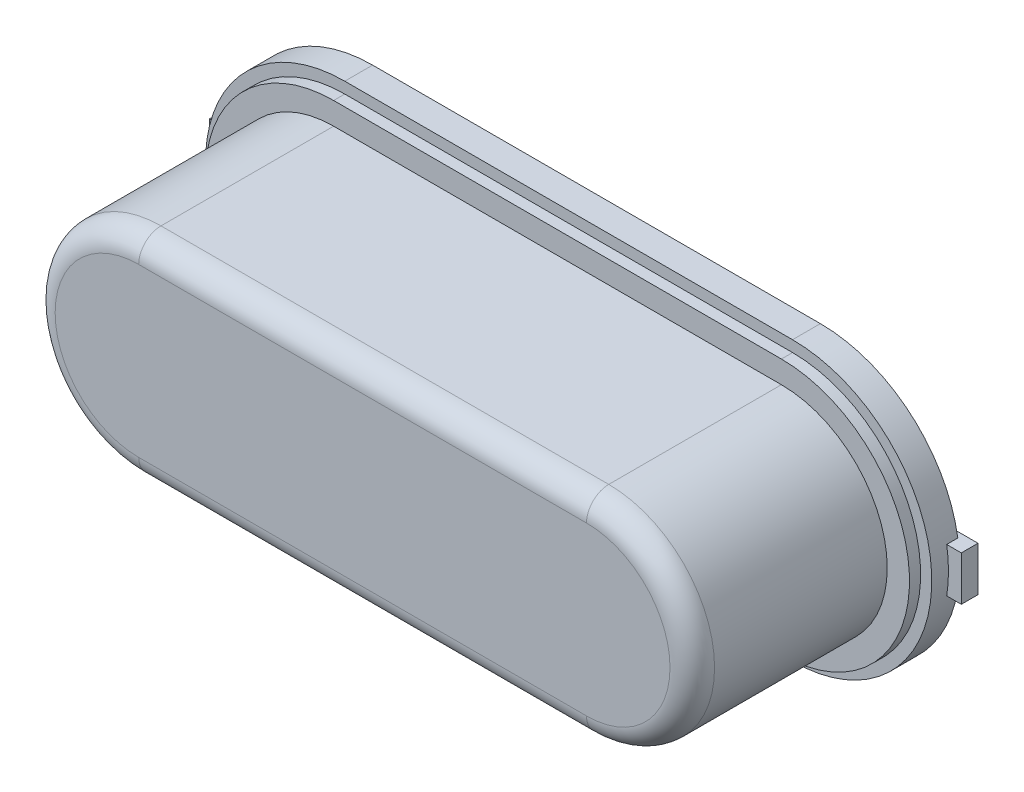
SolidWorks part; units mm, degrees
material "1023 Carbon Steel Sheet (SS)"
ref_plane "Front Plane" through (0, 0, 0) normal (0, 0, 1) x (1, 0, 0)
ref_plane "Top Plane" through (0, 0, 0) normal (0, 1, 0) x (1, 0, 0)
ref_plane "Right Plane" through (0, 0, 0) normal (1, 0, 0) x (0, 0, -1)
sketch "Sketch1" plane through (0, 0, 0) normal (0, 0, 1) x (1, 0, 0)
  line L0 (-4.02, 0) -> (4.02, 0) construction
  line L1 (-4.02, 2.5) -> (4.02, 2.5)
  line L2 (-4.02, -2.5) -> (4.02, -2.5)
  arc A0 (-4.02, 2.5) -> (-4.02, -2.5) centre (-4.02, 0) ccw
  arc A1 (4.02, -2.5) -> (4.02, 2.5) centre (4.02, 0) ccw
  point P3 (0, 0)
  point P8 (-1.52, 0)
  point P9 (1.52, 0)
extrude "Boss-Extrude1" add sketch "Sketch1" along normal blind 4.3
sketch "Sketch2" plane through (0, 0, 0) normal (0, 0, 1) x (1, 0, 0)
  line L0 (-4.02, 0) -> (4.02, 0) construction
  line L1 (-4.02, 1.9) -> (4.02, 1.9)
  line L2 (-4.02, -1.9) -> (4.02, -1.9)
  arc A0 (-4.02, 1.9) -> (-4.02, -1.9) centre (-4.02, 0) ccw
  arc A1 (4.02, -1.9) -> (4.02, 1.9) centre (4.02, 0) ccw
  point P4 (0, 0)
  dimension "D1" = 3.8
extrude "Cut-Extrude1" cut sketch "Sketch2" along normal through all from offset 0.8 flip side to cut
fillet "Fillet1" radius 0.4 4 edges at (0, 1.9, 4.3) (5.92, 0, 4.3) (0, -1.9, 4.3) (-5.92, 0, 4.3)
sketch "Sketch3" plane through (0, 0, 0) normal (0, 0, 1) x (1, 0, 0)
  line L0 (-4.02, 0) -> (4.02, 0) construction
  line L1 (-4.02, 2.3) -> (4.02, 2.3)
  line L2 (-4.02, -2.3) -> (4.02, -2.3)
  line L3 (4.02, 2.5) -> (-4.02, 2.5) construction
  arc A0 (-4.02, 2.3) -> (-4.02, -2.3) centre (-4.02, 0) ccw
  arc A1 (4.02, -2.3) -> (4.02, 2.3) centre (4.02, 0) ccw
  point P4 (0, 0)
  dimension "D1" = 0.2
extrude "Cut-Extrude2" cut sketch "Sketch3" along normal through all from offset 0.6 flip side to cut
sketch "Sketch5" plane through (0, 0, 0) normal (0, 0, 1) x (1, 0, 0)
  line L1 (-7.3546, 3.5276) -> (7.8493, 3.5276)
  line L2 (-7.3546, 3.5276) -> (-7.3546, -4.0743)
  line L3 (-7.3546, -4.0743) -> (7.8493, -4.0743)
  line L4 (7.8493, 3.5276) -> (7.8493, -4.0743)
extrude "Cut-Extrude3" cut sketch "Sketch5" along normal blind 0.1
sketch "Sketch6" plane through (0, 0, 0) normal (0, 0, 1) x (1, 0, 0)
  line L0 (-2.2, 0) -> (2.2, 0) construction
  line L1 (-6.75, 0.4) -> (-2.2, 0.4)
  line L2 (-6.75, 0.4) -> (-6.75, -0.4)
  line L3 (-6.75, -0.4) -> (-2.2, -0.4)
  line L4 (-2.2, 0.4) -> (-2.2, -0.4)
  line L5 (2.2, 0.4) -> (6.75, 0.4)
  line L6 (2.2, 0.4) -> (2.2, -0.4)
  line L7 (2.2, -0.4) -> (6.75, -0.4)
  line L8 (6.75, 0.4) -> (6.75, -0.4)
  point P10 (0, 0)
  dimension "D1" = 13.5
  dimension "D2" = 0.8
  dimension "D3" = 4.4
extrude "Boss-Extrude2" add sketch "Sketch6" along normal blind 0.3
